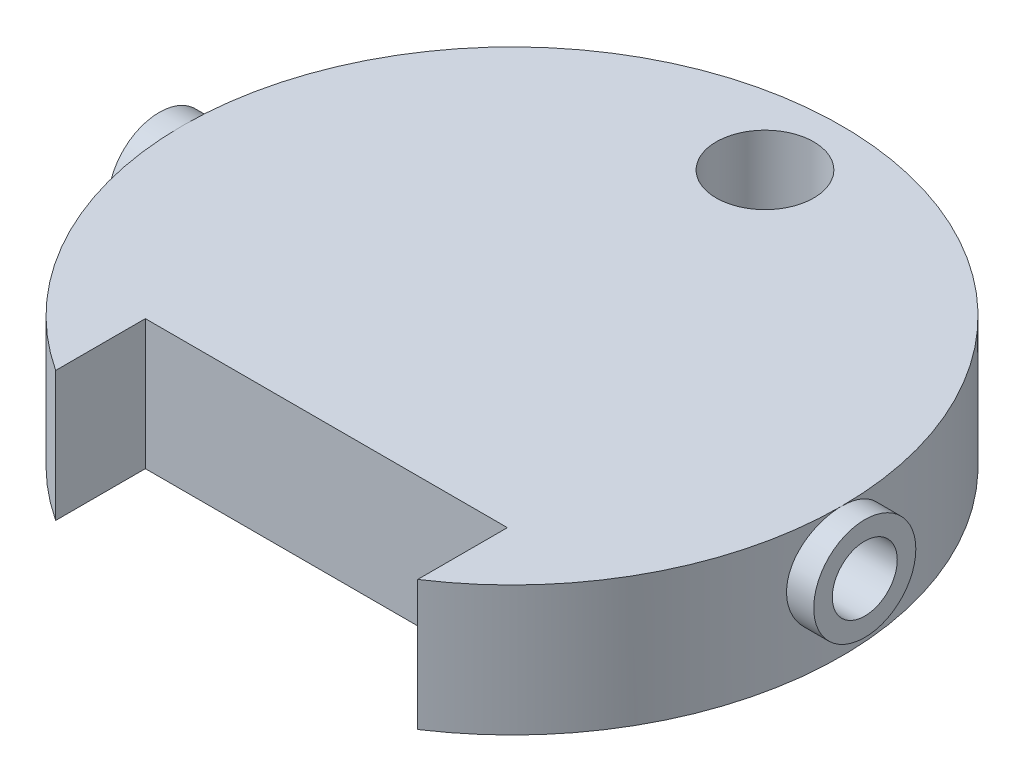
SolidWorks part; units mm, degrees
ref_plane "Front Plane" through (0, 0, 0) normal (0, 0, 1) x (1, 0, 0)
ref_plane "Top Plane" through (0, 0, 0) normal (0, 1, 0) x (1, 0, 0)
ref_plane "Right Plane" through (0, 0, 0) normal (1, 0, 0) x (0, 0, -1)
sketch "Sketch1" plane through (0, 0, 0) normal (0, 1, 0) x (1, 0, 0)
  line L0 (-2.2042, 3.55) -> (2.2205, 3.55) construction
  line L1 (-3.1315, 3.25) -> (3.2128, 3.25) construction
  line L2 (0, 0) -> (0, -5.3682) construction
  line L4 (-1.95, -2.9665) -> (-1.95, -2)
  line L5 (-1.95, -2) -> (1.95, -2)
  line L6 (1.95, -2.9665) -> (1.95, -2)
  line L7 (-6.645, 0) -> (9.123, 0) construction
  line L9 (-2.65, 0.5) -> (2.65, 0.5)
  line L10 (-2.65, 0.5) -> (-2.65, -0.5)
  line L11 (-2.65, -0.5) -> (2.65, -0.5)
  line L12 (2.65, 0.5) -> (2.65, -0.5)
  arc A0 (1.95, -2.9665) -> (3.4803, -0.7) centre (0, 0) ccw
  circle A1 centre (0, 2.725) radius 0.525
  arc A2 (-3.4803, -0.7) -> (-1.95, -2.9665) centre (0, 0) ccw
  arc A3 (3.4803, -0.7) -> (-3.4803, -0.7) centre (0, 0) ccw
  dimension "D1" = 7.1
  dimension "D2" = 1.05
  dimension "D3" = 0.3
  dimension "D4" = 3.9
  dimension "D5" = 2
  dimension "D6" = 1
  dimension "D7" = 5.3
extrude "Boss-Extrude1" add sketch "Sketch1" along normal blind 0.55 and the other way blind 0.85
sketch "Sketch2" plane through (0, 0, 0) normal (1, 0, 0) x (0, 0, -1)
  circle A0 centre (0, 0) radius 0.35
  dimension "D1" = 0.7
extrude "Cut-Extrude1" cut sketch "Sketch2" against normal through all and the other way through all
ref_plane "Plane1" through (3.8, 0, 0) normal (1, 0, 0) x (0, 0, -1)
sketch "Sketch3" plane through (3.8, 0, 0) normal (1, 0, 0) x (0, 0, -1)
  line L0 (3.55, 0.55) -> (-2.9665, 0.55) construction
  circle A0 centre (0, 0) radius 0.55
  circle A1 centre (0, 0) radius 0.35 construction
  circle A2 centre (0, 0) radius 0.35
extrude "Boss-Extrude2" add sketch "Sketch3" against normal up to next
mirror "Mirror1" about plane through (0, 0, 0) normal (1, 0, 0) of "Boss-Extrude2"
sketch "Sketch4" plane through (0, 0.55, 0) normal (0, 1, 0) x (1, 0, 0)
  line L0 (-2.1, -2.6739) -> (-2.1, -1.85)
  line L1 (-2.1, -1.85) -> (2.1, -1.85)
  line L2 (2.1, -1.85) -> (2.1, -2.6739)
  line L3 (-1.95, -2.9665) -> (-1.95, -2)
  line L4 (-1.95, -2) -> (1.95, -2)
  line L5 (1.95, -2) -> (1.95, -2.9665)
  line L6 (-1.95, -2.9665) -> (-1.95, -2)
  line L7 (-1.95, -2) -> (1.95, -2)
  line L8 (1.95, -2) -> (1.95, -2.9665)
  arc A0 (2.1, -2.6739) -> (3.4, 0) centre (0, 0) ccw
  arc A1 (3.4, 0) -> (-3.4, 0) centre (0, 0) ccw
  arc A2 (-3.4, 0) -> (-2.1, -2.6739) centre (0, 0) ccw
  arc A3 (1.95, -2.9665) -> (3.55, 0) centre (0, 0) ccw
  arc A4 (3.55, 0) -> (-3.55, 0) centre (0, 0) ccw
  arc A5 (-3.55, 0) -> (-1.95, -2.9665) centre (0, 0) ccw
  arc A6 (1.95, -2.9665) -> (3.55, 0) centre (0, 0) ccw
  arc A7 (3.55, 0) -> (-3.55, 0) centre (0, 0) ccw
  arc A8 (-3.55, 0) -> (-1.95, -2.9665) centre (0, 0) ccw
  dimension "D1" = 0
  dimension "D2" = 0.15
sketch "Sketch5" plane through (0, 0.55, 0) normal (0, 1, 0) x (1, 0, 0)
  line L1 (-2.65, 0.5) -> (2.65, 0.5)
  line L2 (-2.65, 0.5) -> (-2.65, -0.5)
  line L3 (-2.65, -0.5) -> (2.65, -0.5)
  line L4 (2.65, 0.5) -> (2.65, -0.5)
extrude "Boss-Extrude3" add sketch "Sketch5" against normal blind 0.1
